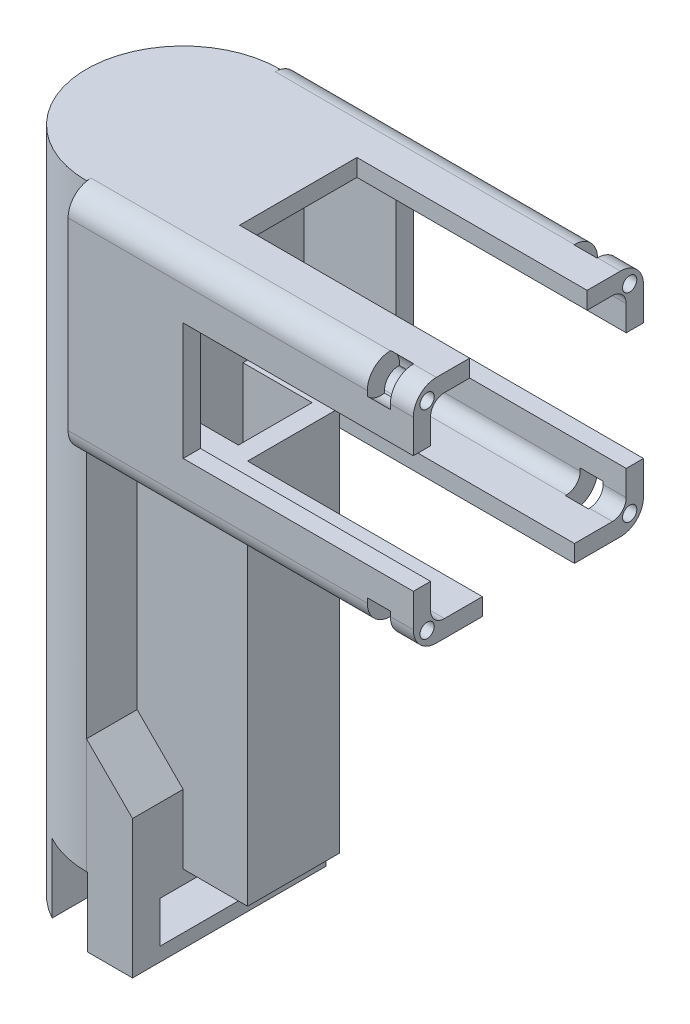
SolidWorks part; units mm, degrees
ref_plane "前视基准面" through (0, 0, 0) normal (0, 0, 1) x (1, 0, 0)
ref_plane "上视基准面" through (0, 0, 0) normal (0, 1, 0) x (1, 0, 0)
ref_plane "右视基准面" through (0, 0, 0) normal (1, 0, 0) x (0, 0, -1)
sketch "Sketch1" plane through (0, 0, 0) normal (1, 0, 0) x (0, 0, -1)
  line L1 (-25, -25) -> (25, -25)
  line L2 (-25, -25) -> (-25, 25)
  line L3 (-25, 25) -> (25, 25)
  line L4 (25, -25) -> (25, 25)
  line L5 (-25, -25) -> (25, 25) construction
  line L6 (-25, 25) -> (25, -25) construction
  point P0 (0, 0)
  dimension "D1" = 50
  dimension "D2" = 50
extrude "Boss-Extrude1" add sketch "Sketch1" against normal blind 75
fillet "Fillet1" radius 5 4 edges at (-37.5, -25, 25) (-37.5, -25, -25) (-37.5, 25, -25) (-37.5, 25, 25)
sketch "Sketch2" plane through (0, 0, 0) normal (1, 0, 0) x (0, 0, -1)
  line L1 (-21.25, -21.25) -> (21.25, -21.25)
  line L2 (-21.25, -21.25) -> (-21.25, 21.25)
  line L3 (-21.25, 21.25) -> (21.25, 21.25)
  line L4 (21.25, -21.25) -> (21.25, 21.25)
  line L5 (-21.25, -21.25) -> (21.25, 21.25) construction
  line L6 (-21.25, 21.25) -> (21.25, -21.25) construction
  point P0 (0, 0)
  dimension "D1" = 42.5
  dimension "D2" = 42.5
extrude "Cut-Extrude1" cut sketch "Sketch2" against normal blind 70
fillet "Fillet2" radius 3 4 edges at (-35, -21.25, 21.25) (-35, -21.25, -21.25) (-35, 21.25, -21.25) (-35, 21.25, 21.25)
sketch "Sketch3" plane through (0, 0, 0) normal (1, 0, 0) x (0, 0, -1)
  line L0 (20, 25) -> (-20, 25) construction
  line L1 (-12.75, 25) -> (12.75, 25)
  line L2 (-12.75, 25) -> (-12.75, 21.25)
  line L3 (-12.75, 21.25) -> (12.75, 21.25)
  line L4 (12.75, 25) -> (12.75, 21.25)
  line L5 (18.25, 21.25) -> (-18.25, 21.25) construction
  line L6 (-25, 20) -> (-25, -20) construction
  line L7 (-25, 12.75) -> (-21.25, 12.75)
  line L8 (-25, 12.75) -> (-25, -12.75)
  line L9 (-25, -12.75) -> (-21.25, -12.75)
  line L10 (-21.25, 12.75) -> (-21.25, -12.75)
  line L11 (-21.25, 18.25) -> (-21.25, -18.25) construction
  line L12 (21.25, -18.25) -> (21.25, 18.25) construction
  line L13 (21.25, 12.75) -> (25, 12.75)
  line L14 (21.25, 12.75) -> (21.25, -12.75)
  line L15 (21.25, -12.75) -> (25, -12.75)
  line L16 (25, 12.75) -> (25, -12.75)
  line L17 (25, -20) -> (25, 20) construction
  line L18 (21.25, -18.25) -> (21.25, 18.25) construction
  line L19 (18.25, 21.25) -> (-18.25, 21.25) construction
  dimension "D1" = 25.5
  dimension "D2" = 25.5
  dimension "D3" = 25.5
  dimension "D4" = 8.5
  dimension "D5" = 8.5
  dimension "D6" = 8.5
extrude "Cut-Extrude2" cut sketch "Sketch3" against normal blind 50
sketch "Sketch4" plane through (0, 0, 0) normal (1, 0, 0) x (0, 0, -1)
  line L0 (0, 0) -> (0, -25) construction
  line L1 (-20, -25) -> (20, -25) construction
  line L2 (-18.25, -21.25) -> (18.25, -21.25) construction
  line L3 (-10, -21.25) -> (10, -21.25)
  line L4 (-10, -21.25) -> (-10, -25)
  line L5 (-10, -25) -> (10, -25)
  line L6 (10, -21.25) -> (10, -25)
  dimension "D1" = 20
  dimension "D2" = 10
extrude "Cut-Extrude3" cut sketch "Sketch4" against normal blind 70
sketch "Sketch8" plane through (0, 0, 0) normal (1, 0, 0) x (0, 0, -1)
  line L0 (-12.75, 25) -> (-20, 25) construction
  line L1 (-25, 20) -> (-25, 12.75) construction
  circle A0 centre (-22, 21.6) radius 1.55
  dimension "D1" = 3.1
  dimension "D2" = 3.4
  dimension "D3" = 3
extrude "Cut-Extrude5" cut sketch "Sketch8" against normal blind 5
sketch "Sketch9" plane through (-5, 0, 0) normal (1, 0, 0) x (0, 0, -1)
  circle A0 centre (-22, 21.6) radius 4
  dimension "D1" = 8
extrude "Cut-Extrude6" cut sketch "Sketch9" against normal blind 5
mirror "Mirror1" about plane through (0, 0, 0) normal (0, 1, 0) of "Cut-Extrude5", "Cut-Extrude6"
mirror "Mirror2" about plane through (0, 0, 0) normal (0, 0, 1) of "Mirror1", "Cut-Extrude5", "Cut-Extrude6"
sketch "Sketch10" plane through (0, 0, 0) normal (0, 1, 0) x (1, 0, 0)
  line L0 (-75, -20) -> (-75, 20) construction
  line L1 (-75, -21) -> (-75, 21)
  arc A0 (-75, -21) -> (-75, 21) centre (-75, 0) cw
  dimension "D1" = 21
extrude "Boss-Extrude2" add sketch "Sketch10" along normal blind 25 and the other way blind 120
sketch "Sketch11" plane through (0, -120, 0) normal (0, -1, 0) x (1, 0, 0)
  line L0 (-85, 18.4662) -> (-85, -18.4662)
  line L1 (-75, 20) -> (-75, -20) construction
  line L2 (-75, 21) -> (-75, -21)
  arc A0 (-75, 21) -> (-75, -21) centre (-75, 0) ccw construction
  arc A1 (-75, 21) -> (-85, 18.4662) centre (-75, 0) ccw
  arc A2 (-85, -18.4662) -> (-75, -21) centre (-75, 0) ccw
  dimension "D1" = 10
extrude "Cut-Extrude8" cut sketch "Sketch11" against normal blind 15
sketch "Sketch12" plane through (-85, 0, 0) normal (1, 0, 0) x (0, 0, -1)
  line L0 (-18.4662, -112.5) -> (18.4662, -112.5) construction
  line L1 (-18.4662, -105) -> (-18.4662, -120) construction
  line L2 (18.4662, -105) -> (18.4662, -120) construction
  circle A0 centre (0, -112.5) radius 1.55
  circle A1 centre (-6.5, -112.5) radius 1.55
  circle A2 centre (6.5, -112.5) radius 1.55
  dimension "D1" = 3.1
  dimension "D2" = 6.5
  dimension "D3" = 6.5
extrude "Cut-Extrude9" cut sketch "Sketch12" against normal blind 15
sketch "Sketch13" plane through (0, -105, 0) normal (0, -1, 0) x (1, 0, 0)
  line L1 (-75, 21) -> (-65, 21)
  line L2 (-75, 21) -> (-75, -21)
  line L3 (-75, -21) -> (-65, -21)
  line L4 (-65, 21) -> (-65, -21)
  dimension "D1" = 10
  dimension "D2" = 42
extrude "Boss-Extrude3" add sketch "Sketch13" along normal blind 15 and the other way blind 15 separate body
sketch "Sketch15" plane through (0, 0, 21) normal (0, 0, 1) x (1, 0, 0)
  line L0 (-65, -90) -> (-75, -90)
  line L1 (-75, -90) -> (-75, -80)
  line L2 (-75, -105) -> (-75, -24.899) construction
  line L3 (-75, -80) -> (-65, -90)
  dimension "D1" = 10
extrude "Boss-Extrude4" add sketch "Sketch15" against normal blind 42
sketch "Sketch16" plane through (-65, 0, 0) normal (1, 0, 0) x (0, 0, -1)
  line L0 (21, -105) -> (-21, -105) construction
  line L1 (-15, -108) -> (15, -108)
  line L2 (-15, -108) -> (-15, -117)
  line L3 (-15, -117) -> (15, -117)
  line L4 (15, -108) -> (15, -117)
  line L5 (21, -120) -> (-21, -120) construction
  line L6 (21, -90) -> (21, -120) construction
  line L7 (-21, -90) -> (-21, -120) construction
  dimension "D1" = 3
  dimension "D2" = 3
  dimension "D3" = 6
  dimension "D4" = 6
extrude "Cut-Extrude10" cut sketch "Sketch16" against normal blind 10
sketch "Sketch17" plane through (0, -120, 0) normal (0, -1, 0) x (1, 0, 0)
  line L0 (-75, -21) -> (-65, -21) construction
  line L1 (-75, 21) -> (-74.8, 21)
  line L2 (-75, 21) -> (-75, -21)
  line L3 (-75, -21) -> (-74.8, -21)
  line L4 (-74.8, 21) -> (-74.8, -21)
  dimension "D1" = 0.2
extrude "Cut-Extrude11" cut sketch "Sketch17" against normal blind 15
sketch "Sketch18" plane through (0, -25, 0) normal (0, -1, 0) x (1, 0, 0)
  line L5 (-75, 20) -> (-75, -20) construction
  line L6 (-75, 10) -> (-51, 10)
  line L7 (-75, 10) -> (-75, -10)
  line L8 (-75, -10) -> (-51, -10)
  line L9 (-51, 10) -> (-51, -10)
  line L10 (-70, -10) -> (0, -10) construction
  dimension "D1" = 24
  dimension "D2" = 20
extrude "Boss-Extrude7" add sketch "Sketch18" along normal blind 80 and the other way blind 3.75
sketch "Sketch19" plane through (0, -21.25, 0) normal (0, 1, 0) x (1, 0, 0)
  line L0 (-70, -18.25) -> (-70, 18.25) construction
  line L1 (-70, 8) -> (-55, 8)
  line L2 (-70, 8) -> (-70, -8)
  line L3 (-70, -8) -> (-55, -8)
  line L4 (-55, 8) -> (-55, -8)
  line L5 (-51, 10) -> (0, 10) construction
  dimension "D1" = 15
  dimension "D2" = 16
  dimension "D3" = 2
extrude "Cut-Extrude12" cut sketch "Sketch19" against normal blind 84
